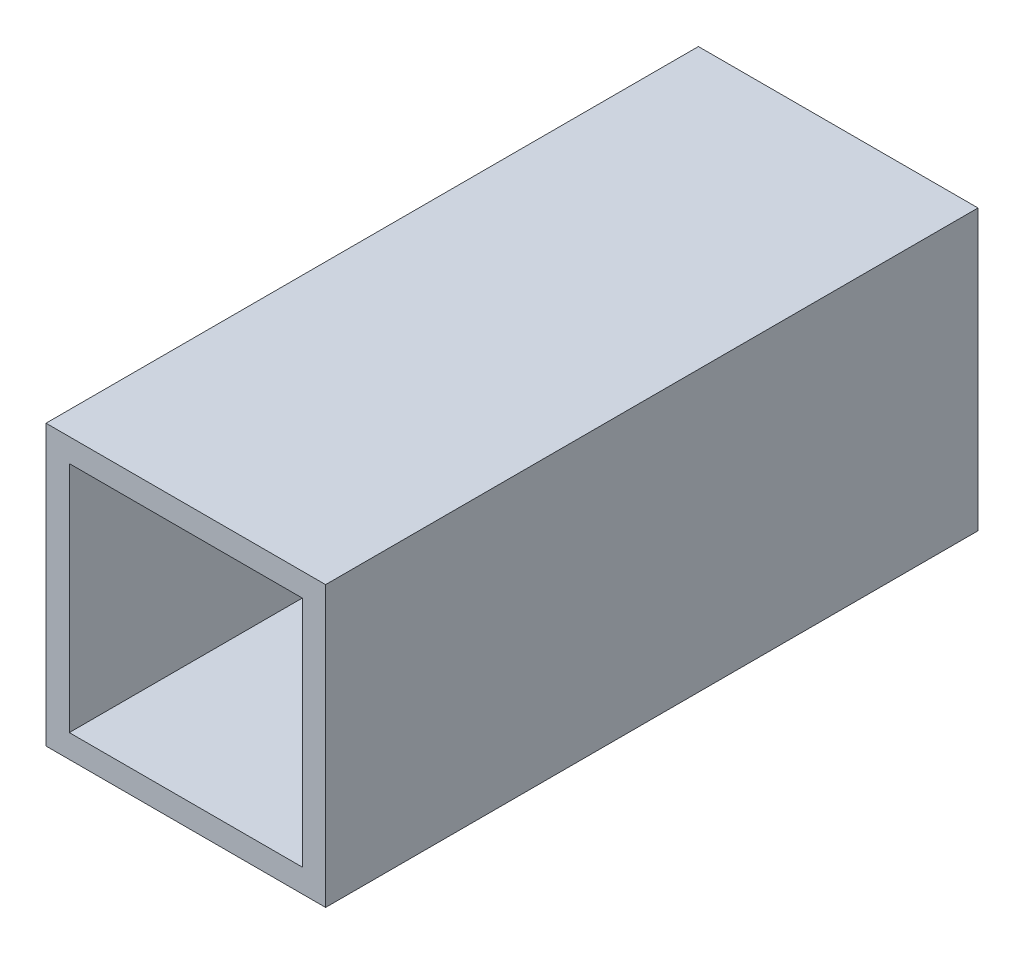
SolidWorks part; units mm, degrees
ref_plane "Alzado" through (0, 0, 0) normal (0, 0, 1) x (1, 0, 0)
ref_plane "Planta" through (0, 0, 0) normal (0, 1, 0) x (1, 0, 0)
ref_plane "Vista lateral" through (0, 0, 0) normal (1, 0, 0) x (0, 0, -1)
sketch "Croquis1" plane through (0, 0, 0) normal (0, 0, 1) x (1, 0, 0)
  line L0 (-7.9375, 7.9375) -> (-7.9375, -7.9375)
  line L1 (9.525, 9.525) -> (-9.525, 9.525)
  line L2 (9.525, 9.525) -> (9.525, -9.525)
  line L3 (9.525, -9.525) -> (-9.525, -9.525)
  line L4 (-9.525, 9.525) -> (-9.525, -9.525)
  line L5 (9.525, 9.525) -> (-9.525, -9.525) construction
  line L6 (9.525, -9.525) -> (-9.525, 9.525) construction
  line L7 (7.9375, -7.9375) -> (-7.9375, -7.9375)
  line L8 (7.9375, 7.9375) -> (7.9375, -7.9375)
  line L9 (7.9375, 7.9375) -> (-7.9375, 7.9375)
  point P0 (0, 0)
  dimension "D1" = 19.05
  dimension "D2" = 19.05
  dimension "D3" = 1.5875
extrude "Saliente-Extruir1" add sketch "Croquis1" along normal mid plane 44.45
